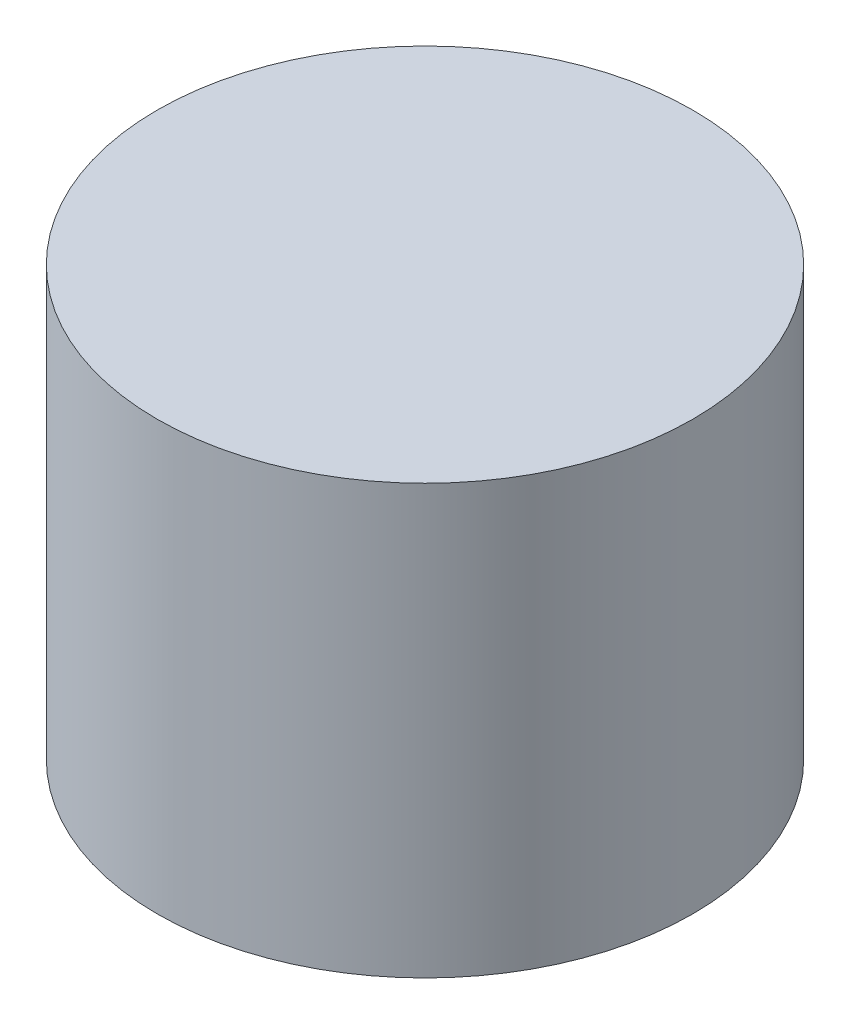
SolidWorks part; units mm, degrees
ref_plane "Front Plane" through (0, 0, 0) normal (0, 0, 1) x (1, 0, 0)
ref_plane "Top Plane" through (0, 0, 0) normal (0, 1, 0) x (1, 0, 0)
ref_plane "Right Plane" through (0, 0, 0) normal (1, 0, 0) x (0, 0, -1)
sketch "Sketch1" plane through (0, 0, 0) normal (0, 1, 0) x (1, 0, 0)
  circle A0 centre (0, 0) radius 63.5
  dimension "D1" = 127
extrude "Boss-Extrude1" add sketch "Sketch1" along normal blind 101.6
